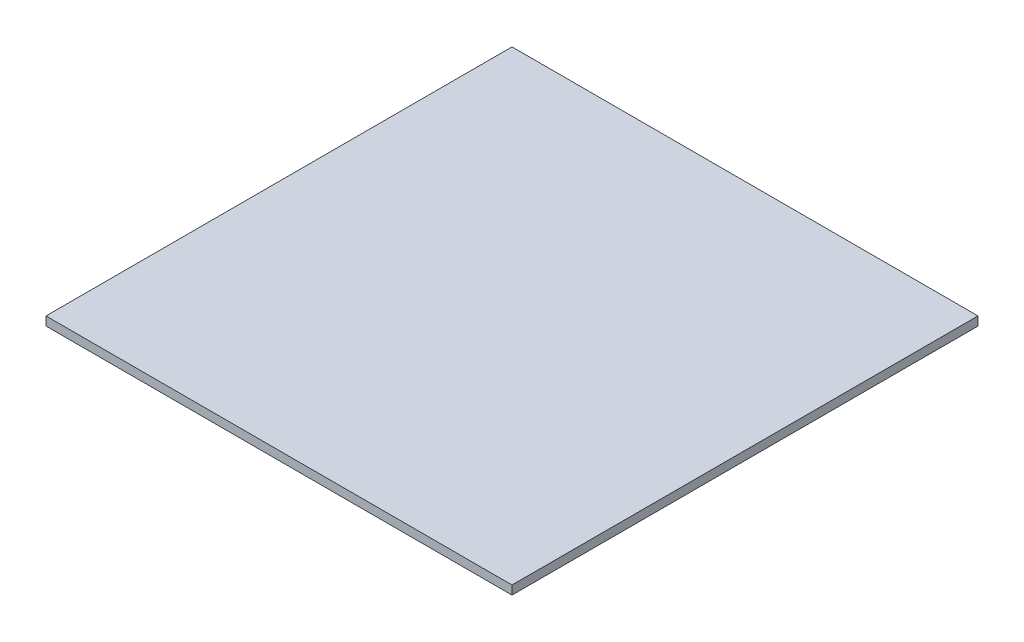
SolidWorks part; units mm, degrees
ref_plane "Front Plane" through (0, 0, 0) normal (0, 0, 1) x (1, 0, 0)
ref_plane "Top Plane" through (0, 0, 0) normal (0, 1, 0) x (1, 0, 0)
ref_plane "Right Plane" through (0, 0, 0) normal (1, 0, 0) x (0, 0, -1)
sketch "Sketch1" plane through (0, 0, 0) normal (0, 1, 0) x (1, 0, 0)
  line L1 (-265, -265) -> (265, -265)
  line L2 (-265, -265) -> (-265, 265)
  line L3 (-265, 265) -> (265, 265)
  line L4 (265, -265) -> (265, 265)
  line L5 (-265, -265) -> (265, 265) construction
  line L6 (-265, 265) -> (265, -265) construction
  point P0 (0, 0)
  dimension "D1" = 530
  dimension "D2" = 530
extrude "Boss-Extrude1" add sketch "Sketch1" along normal blind 10
